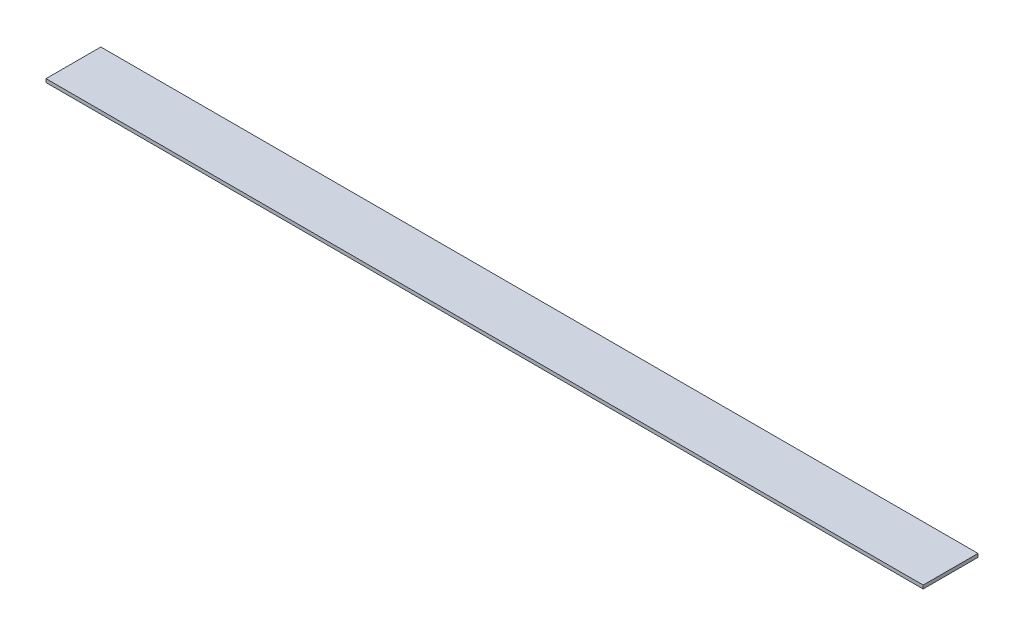
SolidWorks part; units mm, degrees
material "Nylon 101"
ref_plane "Front Plane" through (0, 0, 0) normal (0, 0, 1) x (1, 0, 0)
ref_plane "Top Plane" through (0, 0, 0) normal (0, 1, 0) x (1, 0, 0)
ref_plane "Right Plane" through (0, 0, 0) normal (1, 0, 0) x (0, 0, -1)
sketch "Sketch1" plane through (0, 0, 0) normal (0, 1, 0) x (1, 0, 0)
  line L1 (0, 0) -> (406.4, 0)
  line L2 (0, 0) -> (0, 25.4)
  line L3 (0, 25.4) -> (406.4, 25.4)
  line L4 (406.4, 0) -> (406.4, 25.4)
  dimension "D1" = 25.4
  dimension "D2" = 406.4
extrude "Boss-Extrude1" add sketch "Sketch1" along normal blind 1.5875
